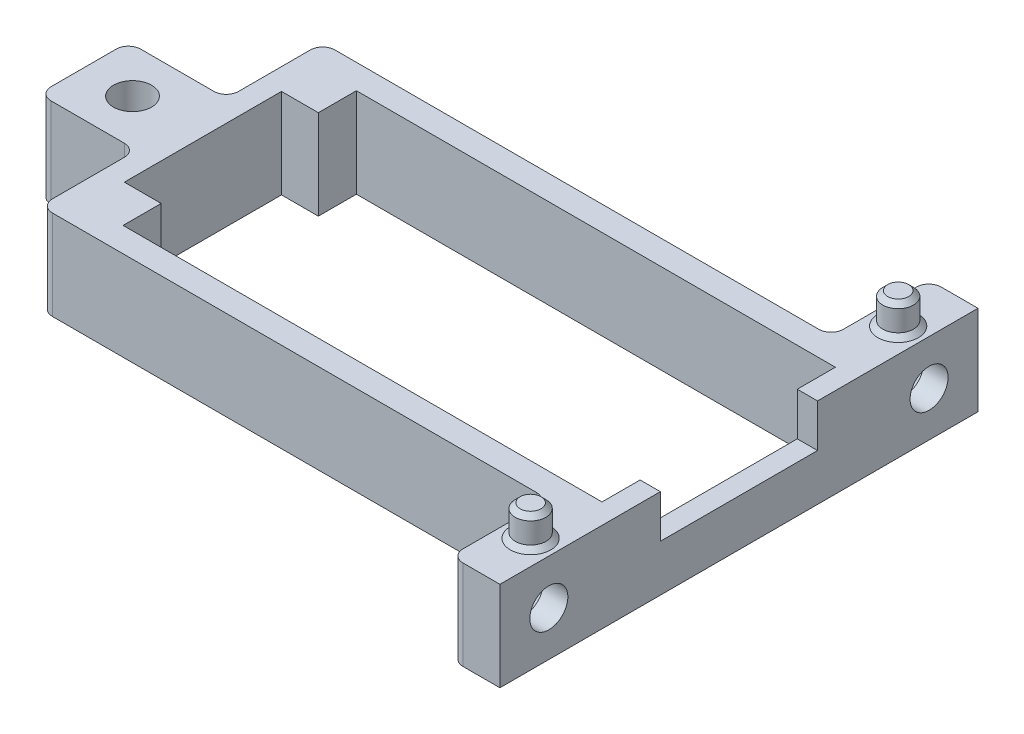
SolidWorks part; units mm, degrees
ref_plane "Front" through (0, 0, 0) normal (0, 0, 1) x (1, 0, 0)
ref_plane "Top" through (0, 0, 0) normal (0, 1, 0) x (1, 0, 0)
ref_plane "Right" through (0, 0, 0) normal (1, 0, 0) x (0, 0, -1)
sketch "Croquis1" plane through (0, 0, 0) normal (0, 1, 0) x (1, 0, 0)
  line L0 (0, 0) -> (0, 6.4) construction
  line L6 (24.25, 11.5) -> (24.25, -11.5) construction
  line L7 (-19.5, 9.5) -> (19.5, 9.5)
  line L8 (-19.5, 9.5) -> (-19.5, 6.4)
  line L9 (-19.5, 6.4) -> (19.5, 6.4) construction
  line L10 (19.5, 9.5) -> (19.5, 6.4)
  line L12 (-21.75, 9) -> (21.75, 9) construction
  line L13 (-21.75, 9) -> (-21.75, -9) construction
  line L14 (-21.75, -9) -> (21.75, -9) construction
  line L15 (21.75, 9) -> (21.75, -9) construction
  line L16 (-21.75, 9) -> (21.75, -9) construction
  line L17 (-21.75, -9) -> (21.75, 9) construction
  line L18 (-24.25, 11.5) -> (-24.25, 3.65)
  line L19 (-50, 0) -> (50, 0) construction
  line L20 (-19.5, -6.4) -> (19.5, -6.4) construction
  line L21 (19.5, -9.5) -> (19.5, -6.4)
  line L22 (-19.5, -9.5) -> (19.5, -9.5)
  line L23 (-19.5, -9.5) -> (-19.5, -6.4)
  line L24 (-24.25, 11.5) -> (21.15, 11.5)
  line L35 (-32.2152, 0) -> (-24.25, 0) construction
  line L36 (0, 0) -> (-24.25, 0) construction
  line L37 (-24.25, -3.65) -> (-32.2152, -3.65)
  line L39 (-24.25, 11.5) -> (24.25, 11.5) construction
  line L40 (-24.25, -3.65) -> (-24.25, -11.5)
  line L51 (-24.25, -11.5) -> (24.25, -11.5) construction
  line L52 (-24.25, -11.5) -> (24.25, -11.5) construction
  line L54 (-22.05, 4) -> (-19.5, 4) construction
  line L55 (-22.05, -4) -> (-17.05, -4) construction
  line L56 (-22.05, -4) -> (-22.05, 4) construction
  line L57 (-22.05, 4) -> (-17.05, 4) construction
  line L58 (-17.05, -4) -> (-17.05, 4) construction
  line L59 (-22.05, -4) -> (-17.05, 4) construction
  line L60 (-22.05, 4) -> (-17.05, -4) construction
  line L61 (-19.5, 4) -> (-19.5, 9.5) construction
  line L62 (-22.05, -4) -> (-19.5, -4) construction
  line L67 (-24.25, -11.5) -> (21.15, -11.5)
  line L68 (24.25, -11.5) -> (21.15, -11.5) construction
  line L69 (24.25, -11.5) -> (24.25, 11.5) construction
  line L71 (21.15, -11.5) -> (21.15, 11.5)
  line L77 (19.5, 6.4) -> (19.5, -6.4)
  line L78 (-19.5, -6.4) -> (-22.5, -6.4)
  line L79 (-22.5, -6.4) -> (-22.5, 6.4)
  line L80 (-22.5, 6.4) -> (-19.5, 6.4)
  line L82 (-24.25, 3.65) -> (-32.2152, 3.65)
  line L83 (-32.2152, -3.65) -> (-32.2152, 3.65)
  line L84 (-32.2152, -3.65) -> (-24.25, 3.65) construction
  line L85 (-24.25, 11.5) -> (-24.25, -11.5) construction
  line L86 (-25.75, 0) -> (-26.9913, 2.15) construction
  line L87 (-26.9913, 2.15) -> (-29.4739, 2.15) construction
  line L88 (-29.4739, 2.15) -> (-30.7152, 0) construction
  line L89 (-30.7152, 0) -> (-29.4739, -2.15) construction
  line L90 (-29.4739, -2.15) -> (-26.9913, -2.15) construction
  line L91 (-26.9913, -2.15) -> (-25.75, 0) construction
  line L92 (-24.25, 0) -> (-24.25, 3.65) construction
  circle A5 centre (-28.2326, 0) radius 1.55
  circle A6 centre (-28.2326, 0) radius 2.15 construction
  point P0 (0, 0)
  point P52 (-19.55, 0)
  dimension "D14" = 1.5
  dimension "D7" = 3.1
  dimension "D1" = 43.5
  dimension "D2" = 18
  dimension "D4" = 39
  dimension "D5" = 3.1
  dimension "D6" = 0.5
  dimension "D8" = 4.3
  dimension "D9" = 1.5
  dimension "D10" = 5
  dimension "D11" = 0.3
  dimension "D12" = 5
  dimension "D13" = 0.6
  dimension "D15" = 3
  dimension "D3" = 2.5
extrude "Saliente-Extruir1" add sketch "Croquis1" along normal blind 7.3
sketch "Croquis4" plane through (0, 0, 0) normal (0, -1, 0) x (1, 0, 0)
  line L32 (-26.9913, 2.15) -> (-25.75, 0) construction
  line L33 (-25.75, 0) -> (-26.9913, -2.15) construction
  line L34 (-26.9913, -2.15) -> (-29.4739, -2.15) construction
  line L35 (-29.4739, -2.15) -> (-30.7152, 0) construction
  line L36 (-30.7152, 0) -> (-29.4739, 2.15) construction
  line L37 (-29.4739, 2.15) -> (-26.9913, 2.15) construction
  line L38 (-26.9913, 2.15) -> (-25.75, 0)
  line L39 (-25.75, 0) -> (-26.9913, -2.15)
  line L40 (-26.9913, -2.15) -> (-29.4739, -2.15)
  line L41 (-29.4739, -2.15) -> (-30.7152, 0)
  line L42 (-30.7152, 0) -> (-29.4739, 2.15)
  line L43 (-29.4739, 2.15) -> (-26.9913, 2.15)
sketch "Croquis5" plane through (21.15, 0, 0) normal (1, 0, 0) x (0, 0, -1)
  line L0 (-6.4, 7.3) -> (-6.4, 0) construction
  line L1 (6.4, 7.3) -> (6.4, 0) construction
  line L2 (-6.4, 7.3) -> (-6.4, 0) construction
  line L3 (6.4, 7.3) -> (6.4, 0) construction
  line L5 (-6.4, 7.3) -> (6.4, 7.3)
  line L6 (-6.4, 7.3) -> (-6.4, 3.8)
  line L7 (-6.4, 3.8) -> (6.4, 3.8)
  line L8 (6.4, 7.3) -> (6.4, 3.8)
  dimension "D1" = 3.5
extrude "Cortar-Extruir4" cut sketch "Croquis5" against normal up to surface (1.65 mm away) up to face at (19.5, 3.65, 0)
extrude "Cortar-Extruir5" cut sketch "Croquis4" against normal blind 5
sketch "Croquis6" plane through (21.15, 0, 0) normal (1, 0, 0) x (0, 0, -1)
  line L2 (19.4652, 7.3) -> (19.4652, 0)
  line L3 (19.4652, 0) -> (11.5, 0)
  line L5 (19.4652, 3.65) -> (13, 3.65) construction
  line L6 (19.4652, 7.3) -> (11.5, 7.3)
  line L7 (13, 3.65) -> (14.2413, 1.5) construction
  line L8 (14.2413, 1.5) -> (16.7239, 1.5) construction
  line L9 (16.7239, 1.5) -> (17.9652, 3.65) construction
  line L10 (17.9652, 3.65) -> (16.7239, 5.8) construction
  line L11 (16.7239, 5.8) -> (14.2413, 5.8) construction
  line L12 (14.2413, 5.8) -> (13, 3.65) construction
  line L17 (0, 50) -> (0, -50) construction
  line L18 (-14.2413, 5.8) -> (-13, 3.65) construction
  line L19 (-16.7239, 5.8) -> (-14.2413, 5.8) construction
  line L20 (-17.9652, 3.65) -> (-16.7239, 5.8) construction
  line L21 (-16.7239, 1.5) -> (-17.9652, 3.65) construction
  line L22 (-14.2413, 1.5) -> (-16.7239, 1.5) construction
  line L23 (-13, 3.65) -> (-14.2413, 1.5) construction
  line L24 (-19.4652, 3.65) -> (-13, 3.65) construction
  line L25 (-11.5, 7.3) -> (-11.5, 0)
  line L26 (-19.4652, 7.3) -> (-11.5, 7.3)
  line L27 (-19.4652, 0) -> (-11.5, 0)
  line L28 (-19.4652, 7.3) -> (-19.4652, 0)
  line L29 (11.5, 0) -> (11.5, 7.3)
  circle A0 centre (15.4826, 3.65) radius 1.55
  circle A1 centre (15.4826, 3.65) radius 2.15 construction
  circle A2 centre (-15.4826, 3.65) radius 2.15 construction
  circle A3 centre (-15.4826, 3.65) radius 1.55
  dimension "D1" = 3.1
  dimension "D2" = 4.3
  dimension "D3" = 1.5
  dimension "D4" = 1.5
  dimension "D5" = 1.5
extrude "Saliente-Extruir2" add sketch "Croquis6" against normal blind 4
sketch "Croquis7" plane through (17.15, 0, 0) normal (-1, 0, 0) x (0, 0, 1)
  line L0 (-17.9652, 3.65) -> (-16.7239, 5.8) construction
  line L1 (-16.7239, 5.8) -> (-14.2413, 5.8) construction
  line L2 (-14.2413, 5.8) -> (-13, 3.65) construction
  line L3 (-13, 3.65) -> (-14.2413, 1.5) construction
  line L4 (-14.2413, 1.5) -> (-16.7239, 1.5) construction
  line L5 (-16.7239, 1.5) -> (-17.9652, 3.65) construction
  line L6 (-17.9652, 3.65) -> (-16.7239, 5.8)
  line L7 (-16.7239, 5.8) -> (-14.2413, 5.8)
  line L8 (-14.2413, 5.8) -> (-13, 3.65)
  line L9 (-13, 3.65) -> (-14.2413, 1.5)
  line L10 (-14.2413, 1.5) -> (-16.7239, 1.5)
  line L11 (-16.7239, 1.5) -> (-17.9652, 3.65)
  line L12 (0, -50) -> (0, 50) construction
  line L13 (16.7239, 1.5) -> (17.9652, 3.65)
  line L14 (14.2413, 1.5) -> (16.7239, 1.5)
  line L15 (13, 3.65) -> (14.2413, 1.5)
  line L16 (14.2413, 5.8) -> (13, 3.65)
  line L17 (16.7239, 5.8) -> (14.2413, 5.8)
  line L18 (17.9652, 3.65) -> (16.7239, 5.8)
extrude "Cortar-Extruir6" cut sketch "Croquis7" against normal blind 2
fillet "Redondeo1" radius 1 10 edges at (17.15, 3.65, 11.5) (-24.25, 3.65, 11.5) (17.15, 3.65, 19.4652) (17.15, 3.65, -19.4652) (17.15, 3.65, -11.5) (-24.25, 3.65, -3.65) (-32.2152, 3.65, 3.65) (-32.2152, 3.65, -3.65) (-24.25, 3.65, 3.65) (-24.25, 3.65, -11.5)
sketch "Croquis8" plane through (0, 7.3, 0) normal (0, 1, 0) x (1, 0, 0)
  line L0 (19.15, -14.9652) -> (21.15, -14.9652) construction
  line L1 (21.15, -19.4652) -> (21.15, -6.4) construction
  line L2 (17.15, -18.4652) -> (21.15, -18.4652) construction
  line L4 (21.15, -18.4652) -> (19.15, -18.4652) construction
  line L5 (19.15, -18.4652) -> (19.15, -14.9652) construction
  line L6 (18.15, -19.4652) -> (21.15, -19.4652) construction
  line L7 (-50, 0) -> (50, 0) construction
  circle A0 centre (19.15, -14.9652) radius 1.25
  circle A1 centre (19.15, 14.9652) radius 1.25
  dimension "D1" = 2.5
  dimension "D2" = 4.5
extrude "Saliente-Extruir3" add sketch "Croquis8" along normal blind 2.5
chamfer "Chaflán1" distance 0.4 angle 45 4 edges at (19.15, 9.8, -16.2152) (19.15, 9.8, 16.2152) (19.15, 7.3, -16.2152) (19.15, 7.3, 16.2152)
